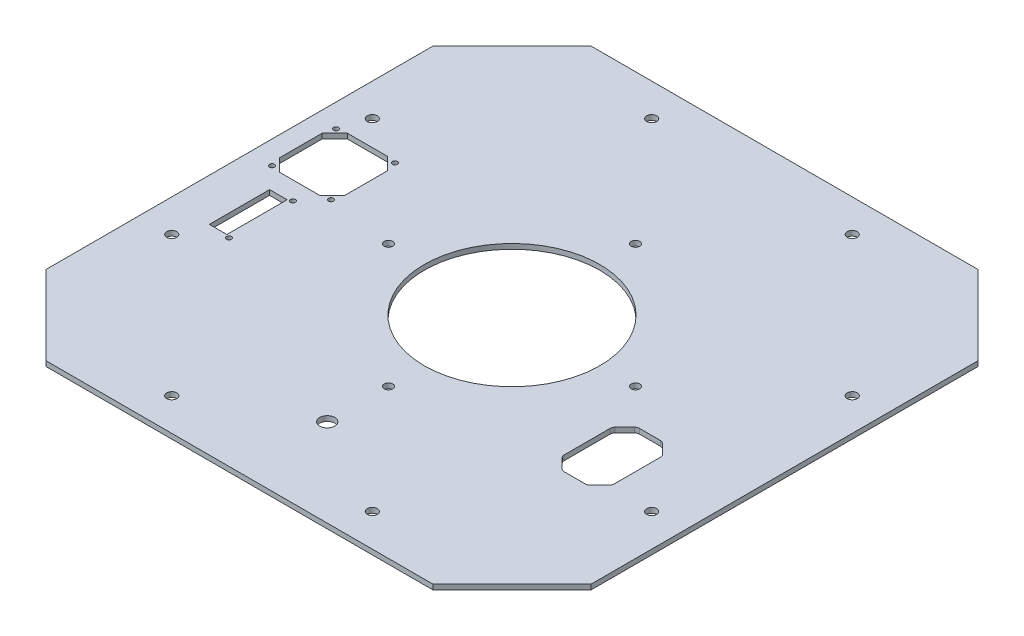
SolidWorks part; units mm, degrees
ref_plane "前视基准面" through (0, 0, 0) normal (0, 0, 1) x (1, 0, 0)
ref_plane "上视基准面" through (0, 0, 0) normal (0, 1, 0) x (1, 0, 0)
ref_plane "右视基准面" through (0, 0, 0) normal (1, 0, 0) x (0, 0, -1)
sketch "草图1" plane through (0, 0, 0) normal (0, 1, 0) x (1, 0, 0)
  line L0 (0, -9.7904) -> (0, 144.5405)
  line L1 (0, 144.5405) -> (31.5269, 176.0674)
  line L2 (31.5269, 176.0674) -> (185.8579, 176.0674)
  line L3 (185.8579, 176.0674) -> (217.3848, 144.5405)
  line L4 (217.3848, 144.5405) -> (217.3848, -9.7904)
  line L5 (217.3848, -9.7904) -> (185.8579, -41.3173)
  line L6 (185.8579, -41.3173) -> (31.5269, -41.3173)
  line L7 (31.5269, -41.3173) -> (0, -9.7904)
  line L8 (31.3198, -41.8173) -> (186.065, -41.8173) construction
  line L10 (217.8848, -9.9975) -> (217.8848, 144.7476) construction
  line L11 (-0.5, 144.7476) -> (15.0563, 160.304) construction
  line L12 (186.065, 176.5674) -> (31.3198, 176.5674) construction
  line L13 (186.065, 176.5674) -> (201.6213, 161.0111) construction
  line L14 (201.6213, -26.261) -> (186.065, -41.8173) construction
  line L15 (15.0563, -25.5539) -> (-0.5, -9.9975) construction
  line L16 (-0.5, 144.7476) -> (-0.5, -9.9975) construction
  circle A0 centre (68.6924, 163.0822) radius 2 construction
  circle A1 centre (148.6924, 163.0822) radius 2 construction
  circle A2 centre (204.3995, 107.3751) radius 2 construction
  circle A3 centre (204.3995, 27.3751) radius 2 construction
  circle A4 centre (148.6924, -28.3321) radius 2 construction
  circle A5 centre (68.6924, -28.3321) radius 2 construction
  circle A6 centre (12.9853, 27.3751) radius 2 construction
  circle A7 centre (12.9853, 107.3751) radius 2 construction
  circle A8 centre (68.6924, 163.0822) radius 2
  circle A9 centre (148.6924, 163.0822) radius 2
  circle A10 centre (204.3995, 107.3751) radius 2
  circle A11 centre (204.3995, 27.3751) radius 2
  circle A12 centre (148.6924, -28.3321) radius 2
  circle A13 centre (68.6924, -28.3321) radius 2
  circle A14 centre (12.9853, 27.3751) radius 2
  circle A15 centre (12.9853, 107.3751) radius 2
  point P25 (7.2782, -17.7757)
  dimension "D1" = 0.5
  dimension "D2" = 0.5
  dimension "D3" = 0.5
  dimension "D4" = 0.5
  dimension "D5" = 0.5
  dimension "D6" = 0.5
  dimension "D7" = 0.5
  dimension "D8" = 0.5
extrude "凸台-拉伸1" add sketch "草图1" along normal blind 2
sketch "草图2" plane through (0, 2, 0) normal (0, 1, 0) x (1, 0, 0)
  line L0 (185.8579, 176.0674) -> (31.5269, 176.0674) construction
  line L1 (29, 97.3751) -> (34, 92.3751)
  line L2 (0, 144.5405) -> (0, -9.7904) construction
  line L3 (217.3848, -9.7904) -> (217.3848, 144.5405) construction
  line L4 (13, 97.3751) -> (29, 97.3751)
  line L5 (8, 92.3751) -> (8, 75.3751)
  line L6 (13, 70.3751) -> (29, 70.3751)
  line L7 (34, 92.3751) -> (34, 75.3751)
  line L8 (29, 70.3751) -> (34, 75.3751)
  line L9 (8, 75.3751) -> (13, 70.3751)
  line L10 (8, 92.3751) -> (13, 97.3751)
  line L11 (31.5269, -41.3173) -> (185.8579, -41.3173) construction
  line L12 (24, 62.3751) -> (17, 62.3751)
  line L13 (24, 62.3751) -> (24, 38.3751)
  line L14 (24, 38.3751) -> (17, 38.3751)
  line L15 (17, 62.3751) -> (17, 38.3751)
  line L16 (173.2132, 23.6827) -> (181.5563, 23.6827)
  line L17 (167.3848, 29.5111) -> (167.3848, 47.8542)
  line L18 (173.2132, 53.6827) -> (181.5563, 53.6827)
  line L19 (187.3848, 29.5111) -> (187.3848, 47.8542)
  line L20 (167.9706, 28.0969) -> (171.799, 24.2685)
  line L21 (182.9706, 24.2685) -> (186.799, 28.0969)
  line L22 (167.9706, 49.2685) -> (171.799, 53.0969)
  line L23 (182.9706, 53.0969) -> (186.799, 49.2685)
  circle A2 centre (9.25, 96.6251) radius 1
  circle A3 centre (108.6924, 116.6251) radius 1.7
  circle A4 centre (108.6924, 18.1251) radius 1.7
  circle A5 centre (157.9424, 67.3751) radius 1.7
  circle A6 centre (59.4424, 67.3751) radius 1.7
  circle A7 centre (108.6924, 67.3751) radius 35
  circle A8 centre (12.9853, 107.3751) radius 2 construction
  circle A9 centre (32.75, 96.6251) radius 1
  circle A10 centre (32.75, 71.1251) radius 1
  circle A11 centre (9.25, 71.1251) radius 1
  circle A12 centre (25.58, 63.1251) radius 1
  circle A13 centre (25.58, 37.6251) radius 1
  arc A14 (167.9706, 49.2685) -> (167.3848, 47.8542) centre (169.3848, 47.8542) ccw
  arc A15 (171.799, 53.0969) -> (173.2132, 53.6827) centre (173.2132, 51.6827) cw
  arc A16 (182.9706, 53.0969) -> (181.5563, 53.6827) centre (181.5563, 51.6827) ccw
  arc A17 (186.799, 49.2685) -> (187.3848, 47.8542) centre (185.3848, 47.8542) cw
  arc A18 (186.799, 28.0969) -> (187.3848, 29.5111) centre (185.3848, 29.5111) ccw
  arc A19 (182.9706, 24.2685) -> (181.5563, 23.6827) centre (181.5563, 25.6827) cw
  arc A20 (171.799, 24.2685) -> (173.2132, 23.6827) centre (173.2132, 25.6827) ccw
  arc A21 (167.9706, 28.0969) -> (167.3848, 29.5111) centre (169.3848, 29.5111) cw
  circle A22 centre (108.6924, -6.3173) radius 3
  point P0 (8, 97.3751)
  point P4 (108.6924, 176.0674)
  point P5 (34, 70.3751)
  point P6 (8, 70.3751)
  point P7 (34, 97.3751)
  point P28 (217.3848, 67.3751)
  point P40 (21, 97.3751)
  point P41 (34, 83.8751)
  point P46 (20.5, 62.3751)
  point P51 (24, 50.3751)
  point P53 (167.3848, 23.6827)
  point P55 (187.3848, 53.6827)
  point P56 (167.3848, 53.6827)
  point P57 (187.3848, 23.6827)
  point P68 (167.3848, 48.6827)
  point P71 (172.3848, 53.6827)
  point P74 (182.3848, 53.6827)
  point P77 (187.3848, 48.6827)
  point P80 (187.3848, 28.6827)
  point P83 (182.3848, 23.6827)
  point P86 (172.3848, 23.6827)
  point P89 (167.3848, 28.6827)
  dimension "D3" = 27
  dimension "D4" = 8
  dimension "D9" = 3.4
  dimension "D10" = 3.4
  dimension "D11" = 3.4
  dimension "D12" = 3.4
  dimension "D14" = 70
  dimension "D23" = 2
  dimension "D24" = 2
  dimension "D25" = 2
  dimension "D26" = 2
  dimension "D34" = 2
  dimension "D35" = 2
  dimension "D40" = 2
  dimension "D41" = 6
  dimension "D2" = 26
  dimension "D5" = 98.5
  dimension "D6" = 49.25
  dimension "D7" = 98.5
  dimension "D8" = 49.25
  dimension "D13" = 10
  dimension "D15" = 25.5
  dimension "D16" = 23.5
  dimension "D17" = 11.75
  dimension "D18" = 12.75
  dimension "D27" = 24
  dimension "D28" = 7
  dimension "D29" = 8
  dimension "D30" = 17
  dimension "D31" = 25.5
  dimension "D32" = 5.08
  dimension "D33" = 12.75
  dimension "D36" = 30
  dimension "D37" = 20
  dimension "D38" = 65
  dimension "D39" = 30
  dimension "D46" = 35
extrude "切除-拉伸1" cut sketch "草图2" against normal blind 10
